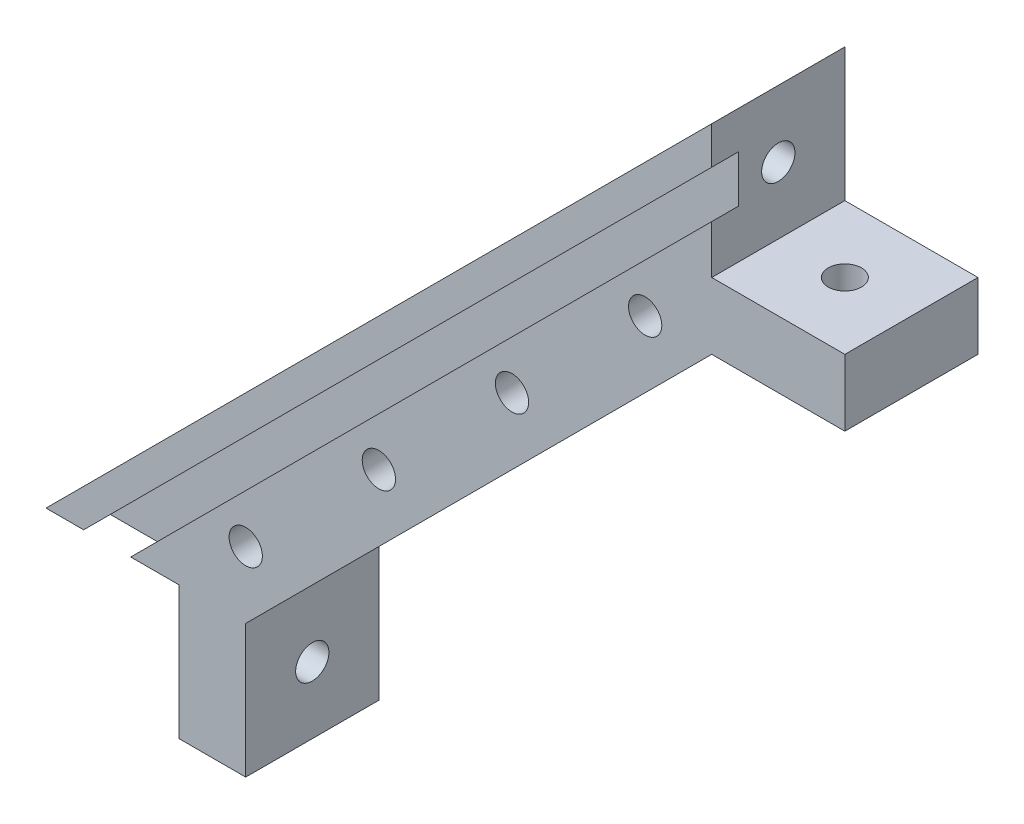
SolidWorks part; units mm, degrees
ref_plane "Front Plane" through (0, 0, 0) normal (0, 0, 1) x (1, 0, 0)
ref_plane "Top Plane" through (0, 0, 0) normal (0, 1, 0) x (1, 0, 0)
ref_plane "Right Plane" through (0, 0, 0) normal (1, 0, 0) x (0, 0, -1)
sketch "Sketch1" plane through (0, 0, 0) normal (0, 0, 1) x (1, 0, 0)
  line L0 (-25, -25) -> (25, 25)
  line L1 (25, 25) -> (25, 15)
  line L2 (-15, -25) -> (-15, -35)
  line L3 (-15, -35) -> (-10, -35)
  line L4 (25, 15) -> (35, 15)
  line L5 (-10, -35) -> (-10, -25)
  line L6 (-25, -25) -> (-15, -25)
  line L7 (-10, -25) -> (25, 10)
  line L8 (25, 10) -> (35, 10)
  line L9 (35, 15) -> (35, 10)
  point P4 (7.5, -7.5)
  point P13 (0, 0)
  dimension "D1" = 45
  dimension "D2" = 10
  dimension "D3" = 5
  dimension "D4" = 40
  dimension "D5" = 70.7107
extrude "Main" add sketch "Sketch1" along normal mid plane 10
sketch "Sketch2" plane through (25, 0, 0) normal (1, 0, 0) x (0, 0, -1)
  line L0 (5, -25) -> (-5, -35) construction
  line L1 (-5, -25) -> (5, -35) construction
  line L2 (-5, 15) -> (5, 25) construction
  line L3 (-5, 25) -> (5, 15) construction
  circle A0 centre (0, -30) radius 1.25
  circle A1 centre (0, 20) radius 1.25
  dimension "D1" = 2.5
extrude "FixHole1" cut sketch "Sketch2" against normal through all
sketch "Sketch3" plane through (0, -25, 0) normal (0, -1, 0) x (-1, 0, 0)
  line L0 (25, 5) -> (15, -5) construction
  line L1 (25, -5) -> (15, 5) construction
  line L2 (15, -5) -> (15, 5) construction
  line L3 (15, 5) -> (10, 5) construction
  line L4 (-25, 5) -> (-35, -5) construction
  line L5 (-25, -5) -> (-35, 5) construction
  line L6 (25, -5) -> (25, 5) construction
  circle A0 centre (20, 0) radius 1.25
  circle A1 centre (-30, 0) radius 1.25
  dimension "D1" = 2.5
extrude "FixHole2" cut sketch "Sketch3" against normal through all
sketch "Sketch4" plane through (0, 0, 5) normal (0, 0, 1) x (1, 0, 0)
  line L0 (25, 22.1716) -> (-22.1716, -25)
  line L1 (-22.1716, -25) -> (-18.636, -25)
  line L2 (-18.636, -25) -> (25, 18.636)
  line L3 (25, 18.636) -> (25, 22.1716)
  line L4 (25, 25) -> (-25, -25) construction
  line L5 (-25, -25) -> (-15, -25) construction
  line L6 (25, 15) -> (25, 25) construction
  dimension "D1" = 2.5
  dimension "D2" = 2
  dimension "D3" = 66.7107
  dimension "D4" = 61.7107
extrude "WindowSlot1" cut sketch "Sketch4" against normal blind 2
sketch "Sketch6" plane through (7.5, -7.5, 0) normal (-0.7071, 0.7071, 0) x (0, 0, 1)
  circle A0 centre (0, 20) radius 1.25
  dimension "D1" = 2.5
  dimension "D2" = 20
extrude "Cut-Extrude2" cut sketch "Sketch6" along normal blind 3
pattern_linear "LPattern1" count 5 spacing 10 along (-0.7071, -0.7071, 0) of "Cut-Extrude2"
sketch "Sketch7" plane through (0, 0, -5) normal (0, 0, -1) x (-1, 0, 0)
  line L0 (15, -25) -> (15, -35) construction
  line L1 (25, -25) -> (15, -25) construction
  circle A0 centre (10, -20) radius 1.25
  point P6 (15, -30)
  point P10 (20, -25)
  dimension "D3" = 2.5
  dimension "D1" = 10
  dimension "D2" = 10
extrude "Cut-Extrude3" cut sketch "Sketch7" against normal through all
pattern_linear "LPattern2" count 4 spacing 14.142 along (0.7071, 0.7071, 0) of "Cut-Extrude3"
